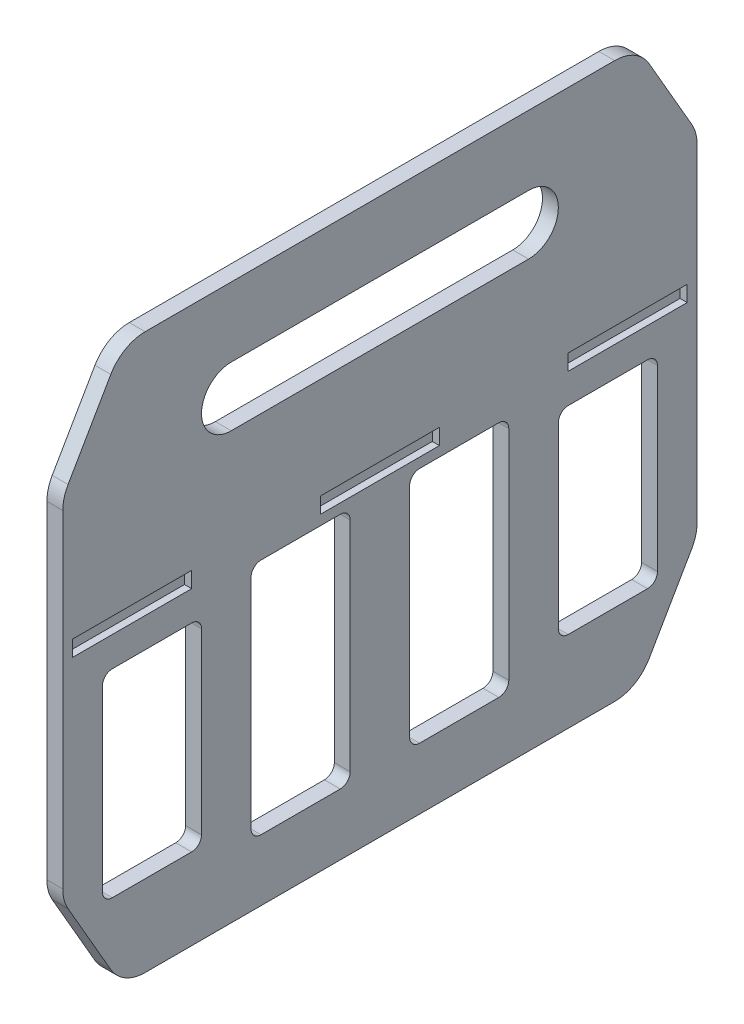
SolidWorks part; units mm, degrees
ref_plane "Front Plane" through (0, 0, 0) normal (0, 0, 1) x (1, 0, 0)
ref_plane "Top Plane" through (0, 0, 0) normal (0, 1, 0) x (1, 0, 0)
ref_plane "Right Plane" through (0, 0, 0) normal (1, 0, 0) x (0, 0, -1)
sketch "Sketch1" plane through (0, 0, 0) normal (1, 0, 0) x (0, 0, -1)
  line L0 (0, 254) -> (0, 0) construction
  line L2 (-203.2, 0) -> (-203.2, 254)
  line L4 (203.2, 0) -> (203.2, 254)
  line L5 (-95.25, 215.9) -> (95.25, 215.9) construction
  line L6 (-95.25, 234.95) -> (95.25, 234.95)
  line L7 (-95.25, 196.85) -> (95.25, 196.85)
  line L8 (-203.2, 127) -> (203.2, 127) construction
  line L10 (-203.2, 169.926) -> (-203.2, 160.274) construction
  line L13 (-203.2, 0) -> (203.2, 0) construction
  line L15 (-203.2, 254) -> (-203.2, 279.4)
  line L16 (-203.2, 279.4) -> (203.2, 279.4)
  line L18 (203.2, 254) -> (203.2, 279.4)
  line L20 (-203.2, 0) -> (-203.2, -76.2)
  line L36 (-203.2, -76.2) -> (203.2, -76.2)
  line L37 (203.2, 0) -> (203.2, -76.2)
  line L39 (203.2, 254) -> (-203.2, 254) construction
  line L40 (-203.2, 12.7) -> (203.2, 12.7) construction
  arc A0 (-95.25, 234.95) -> (-95.25, 196.85) centre (-95.25, 215.9) ccw
  arc A1 (95.25, 196.85) -> (95.25, 234.95) centre (95.25, 215.9) ccw
  point P10 (0, 215.9)
  point P54 (0, 127)
  dimension "D1" = 254
  dimension "D3" = 190.5
  dimension "D4" = 19.05
  dimension "D5" = 38.1
  dimension "D7" = 25.4
  dimension "1" = 76.2
extrude "Boss-Extrude1" add sketch "Sketch1" against normal blind 10.16
sketch "Sketch2" plane through (0, 0, 0) normal (1, 0, 0) x (0, 0, -1)
  line L14 (-203.2, 127) -> (203.2, 127) construction
  line L15 (-196.85, 132.08) -> (-120.65, 132.08)
  line L16 (-196.85, 132.08) -> (-196.85, 121.92)
  line L17 (-196.85, 121.92) -> (-120.65, 121.92)
  line L18 (-120.65, 132.08) -> (-120.65, 121.92)
  line L19 (-203.2, 0) -> (-203.2, 254) construction
  line L20 (-38.1, 132.08) -> (38.1, 132.08)
  line L21 (-38.1, 132.08) -> (-38.1, 121.92)
  line L22 (38.1, 132.08) -> (38.1, 121.92)
  line L23 (-38.1, 121.92) -> (38.1, 121.92)
  line L24 (120.65, 132.08) -> (196.85, 132.08)
  line L25 (120.65, 132.08) -> (120.65, 121.92)
  line L26 (196.85, 132.08) -> (196.85, 121.92)
  line L27 (120.65, 121.92) -> (196.85, 121.92)
  point P6 (-196.85, 127)
  dimension "D1" = 6.35
  dimension "D2" = 10.16
  dimension "D3" = 76.2
  dimension "D4" = 3
extrude "Cut-Extrude1" cut sketch "Sketch2" against normal blind 4.572
chamfer "Chamfer1" distance 38.1 angle 60 4 edges at (-5.08, -76.2, -203.2) (-5.08, 279.4, 203.2) (-5.08, -76.2, 203.2) (-5.08, 279.4, -203.2)
fillet "Fillet1" radius 25.4 8 edges at (-5.08, 279.4, 165.1) (-5.08, 213.4089, 203.2) (-5.08, -10.2089, 203.2) (-5.08, -76.2, 165.1) (-5.08, -76.2, -165.1) (-5.08, -10.2089, -203.2) (-5.08, 213.4089, -203.2) (-5.08, 279.4, -165.1)
sketch "Sketch5" plane through (-10.16, 0, 0) normal (-1, 0, 0) x (0, 0, 1)
  line L0 (-138.2945, 154.178) -> (138.2945, 154.178) construction
  line L3 (203.2, 127) -> (-203.2, 127) construction
  line L5 (-187.96, 154.178) -> (-187.96, 166.878) construction
  line L6 (0, 181.356) -> (0, 127) construction
  line L7 (0, 254) -> (0, 0) construction
  line L8 (-205.74, 127) -> (205.74, 127) construction
  point P8 (-198.882, 154.178)
  point P9 (-177.038, 154.178)
  point P14 (187.96, 166.878)
  point P18 (0, 154.178)
  point P19 (177.038, 154.178)
  point P20 (198.882, 154.178)
  point P21 (198.882, 99.822)
  point P26 (0, 127)
  point P27 (177.038, 99.822)
  point P28 (187.96, 87.122)
  point P29 (-177.038, 99.822)
  point P30 (-198.882, 99.822)
  point P31 (-187.96, 87.122)
  dimension "D1" = 27.178
  dimension "D3" = 21.844
  dimension "D4" = 10.922
  dimension "D5" = 12.7
sketch "Sketch7" plane through (-10.16, 0, 0) normal (-1, 0, 0) x (0, 0, 1)
  point P0 (-198.882, 154.178)
  point P3 (-187.96, 166.878)
  point P6 (-177.038, 154.178)
  point P9 (198.882, 154.178)
  point P12 (177.038, 154.178)
  point P15 (187.96, 166.878)
  point P19 (-177.038, 99.822)
  point P22 (-187.96, 87.122)
  point P25 (-198.882, 99.822)
  point P28 (177.038, 99.822)
  point P31 (187.96, 87.122)
  point P34 (198.882, 99.822)
hole_wizard "CBORE for #3 Socket Head Cap Screw1" positions "Sketch7" profile "Sketch8" counterbore size "#3" standard "ANSI Inch"
sketch "Sketch8" plane through (-10.16, 154.178, -198.882) normal (0, 1, 0) x (0, 0, 1)
  line L0 (0, 0) -> (0, 10.16)
  line L1 (0, 10.16) -> (1.524, 10.16)
  line L3 (1.524, 10.16) -> (1.524, 2.5146)
  line L4 (1.524, 2.5146) -> (2.5794, 2.5146)
  line L5 (2.5794, 2.5146) -> (2.5794, 0)
  line L7 (2.5794, 0) -> (0, 0)
  line L11 (0, -6.35) -> (0, 107.95) construction
  dimension "Thru Hole Dia." = 3.048
  dimension "Thru Hole Depth" = 10.16
  dimension "C'Bore Dia." = 5.1587
  dimension "C'Bore Depth" = 2.5146
sketch "Sketch10" plane through (-10.16, 0, 0) normal (-1, 0, 0) x (0, 0, 1)
  line L0 (196.85, 121.92) -> (120.65, 121.92) construction
  line L1 (149.8806, 121.92) -> (213.3806, 121.92) construction
  line L2 (149.8806, 121.92) -> (149.8806, 20.32) construction
  line L3 (149.8806, 20.32) -> (213.3806, 20.32) construction
  line L4 (213.3806, 121.92) -> (213.3806, 20.32) construction
  line L7 (137.1806, 121.92) -> (117.4936, 121.92) construction
  line L8 (137.1806, 121.92) -> (137.1806, 103.126) construction
  line L9 (137.1806, 103.126) -> (117.4936, 103.126) construction
  line L10 (117.4936, 121.92) -> (117.4936, 103.126) construction
  dimension "D1" = 12.7
  dimension "D2" = 101.6
  dimension "D3" = 63.5
sketch "Sketch11" plane through (0, 0, 0) normal (1, 0, 0) x (0, 0, -1)
  line L7 (-196.85, 121.92) -> (-120.65, 121.92) construction
  line L59 (-171.45, 102.87) -> (-120.65, 102.87)
  line L60 (-177.8, 96.52) -> (-177.8, -17.78)
  line L61 (-171.45, -24.13) -> (-120.65, -24.13)
  line L62 (-114.3, 96.52) -> (-114.3, -17.78)
  line L63 (-76.2, 115.57) -> (-25.4, 115.57)
  line L64 (-82.55, 109.22) -> (-82.55, -30.48)
  line L65 (-76.2, -36.83) -> (-25.4, -36.83)
  line L66 (-19.05, 109.22) -> (-19.05, -30.48)
  line L67 (-196.85, 121.92) -> (-120.65, 121.92) construction
  line L68 (0, -76.2) -> (0, 279.4) construction
  line L69 (-203.2, -76.2) -> (203.2, -76.2) construction
  line L70 (-203.2, 279.4) -> (203.2, 279.4) construction
  line L80 (19.05, 109.22) -> (19.05, -30.48)
  line L81 (76.2, -36.83) -> (25.4, -36.83)
  line L82 (82.55, 109.22) -> (82.55, -30.48)
  line L83 (76.2, 115.57) -> (25.4, 115.57)
  line L88 (114.3, 96.52) -> (114.3, -17.78)
  line L89 (171.45, -24.13) -> (120.65, -24.13)
  line L90 (177.8, 96.52) -> (177.8, -17.78)
  line L91 (171.45, 102.87) -> (120.65, 102.87)
  arc A28 (-120.65, 102.87) -> (-114.3, 96.52) centre (-120.65, 96.52) cw
  arc A29 (-171.45, 102.87) -> (-177.8, 96.52) centre (-171.45, 96.52) ccw
  arc A30 (-177.8, -17.78) -> (-171.45, -24.13) centre (-171.45, -17.78) ccw
  arc A31 (-120.65, -24.13) -> (-114.3, -17.78) centre (-120.65, -17.78) ccw
  arc A32 (-25.4, -36.83) -> (-19.05, -30.48) centre (-25.4, -30.48) ccw
  arc A33 (-82.55, -30.48) -> (-76.2, -36.83) centre (-76.2, -30.48) ccw
  arc A34 (-76.2, 115.57) -> (-82.55, 109.22) centre (-76.2, 109.22) ccw
  arc A35 (-25.4, 115.57) -> (-19.05, 109.22) centre (-25.4, 109.22) cw
  arc A44 (25.4, 115.57) -> (19.05, 109.22) centre (25.4, 109.22) ccw
  arc A45 (76.2, 115.57) -> (82.55, 109.22) centre (76.2, 109.22) cw
  arc A46 (82.55, -30.48) -> (76.2, -36.83) centre (76.2, -30.48) cw
  arc A47 (25.4, -36.83) -> (19.05, -30.48) centre (25.4, -30.48) cw
  arc A52 (120.65, -24.13) -> (114.3, -17.78) centre (120.65, -17.78) cw
  arc A53 (177.8, -17.78) -> (171.45, -24.13) centre (171.45, -17.78) cw
  arc A54 (171.45, 102.87) -> (177.8, 96.52) centre (171.45, 96.52) cw
  arc A55 (120.65, 102.87) -> (114.3, 96.52) centre (120.65, 96.52) ccw
  point P17 (-177.8, 102.87)
  point P20 (-177.8, -24.13)
  point P27 (-82.55, -36.83)
  point P30 (-82.55, 115.57)
  point P63 (82.55, 115.57)
  point P64 (82.55, -36.83)
  point P65 (177.8, -24.13)
  point P67 (177.8, 102.87)
  dimension "D3" = 19.05
  dimension "D6" = 63.5
  dimension "D1" = 6.35
  dimension "D5" = 6.35
  dimension "D2" = 152.4
  dimension "D4" = 127
  dimension "D7" = 19.05
  dimension "D8" = 31.75
  dimension "D9" = 63.5
extrude "Cut-Extrude2" cut sketch "Sketch11" against normal through all
equation "\"D4@Sketch5\"=\"D3@Sketch5\"/2"
